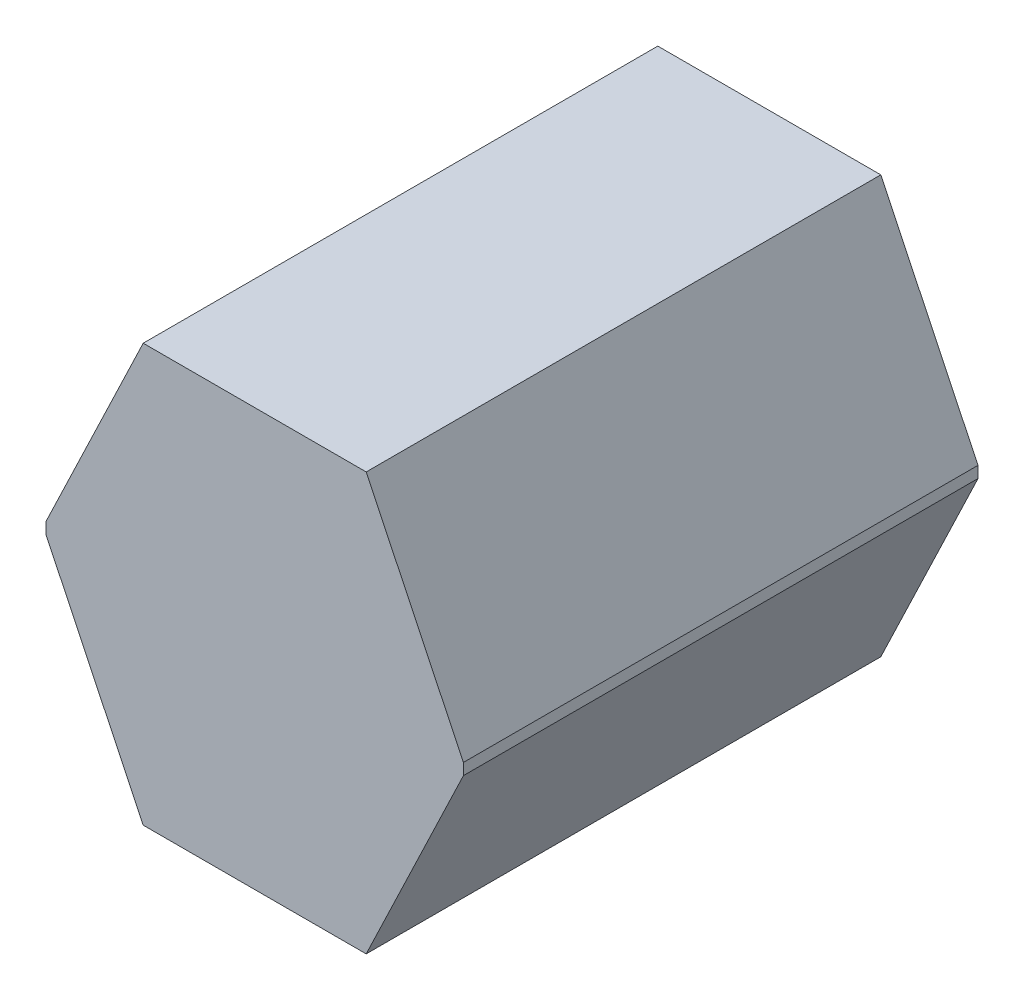
SolidWorks part; units mm, degrees
ref_plane "Ebene vorne" through (0, 0, 0) normal (0, 0, 1) x (1, 0, 0)
ref_plane "Ebene oben" through (0, 0, 0) normal (0, 1, 0) x (1, 0, 0)
ref_plane "Ebene rechts" through (0, 0, 0) normal (1, 0, 0) x (0, 0, -1)
sketch "Skizze1" plane through (0, 0, 0) normal (0, 0, 1) x (1, 0, 0)
  line L0 (-93.8087, 0) -> (105.2679, 0) construction
  line L1 (0, 69.2053) -> (0, -91.1266) construction
  line L2 (97.5, 182.5) -> (-97.5, 182.5)
  line L3 (-97.5, 182.5) -> (-182.5, 5)
  line L4 (-182.5, 5) -> (-182.5, -5)
  line L5 (182.5, 5) -> (182.5, -5)
  line L6 (97.5, 182.5) -> (182.5, 5)
  line L7 (97.5, -182.5) -> (182.5, -5)
  line L8 (-97.5, -182.5) -> (-182.5, -5)
  line L9 (97.5, -182.5) -> (-97.5, -182.5)
  point P12 (0, 182.5)
  point P14 (182.5, 0)
  point P15 (-182.5, 0)
  point P16 (0, -182.5)
  dimension "D1" = 365
  dimension "D2" = 365
  dimension "D3" = 195
  dimension "D4" = 10
extrude "Aufsatz-Linear austragen1" add sketch "Skizze1" along normal blind 450
